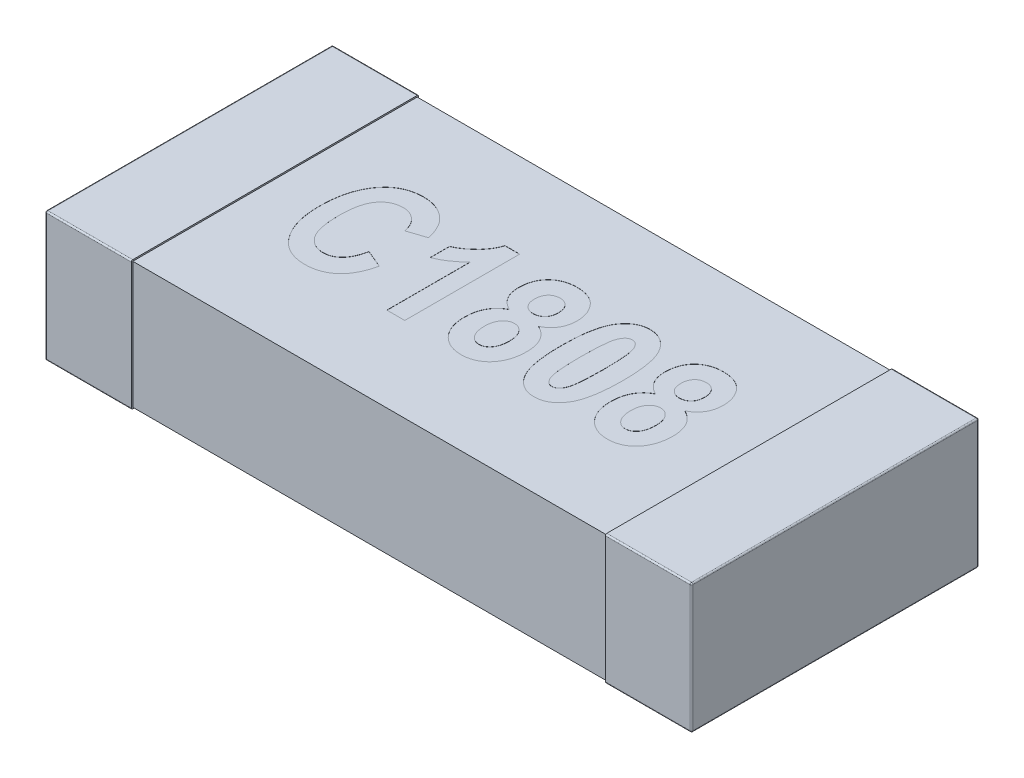
SolidWorks part; units mm, degrees
ref_plane "Front Plane" through (0, 0, 0) normal (0, 0, 1) x (1, 0, 0)
ref_plane "Top Plane" through (0, 0, 0) normal (0, 1, 0) x (1, 0, 0)
ref_plane "Right Plane" through (0, 0, 0) normal (1, 0, 0) x (0, 0, -1)
sketch "Sketch1" plane through (0, 0, 0) normal (0, 1, 0) x (1, 0, 0)
  line L0 (0, 0.15) -> (0, -0.15) construction
  line L1 (-2.25, 0) -> (0, 0) construction
  line L3 (-2.25, 1) -> (-1.65, 1)
  line L4 (-2.25, 1) -> (-2.25, -1)
  line L5 (-2.25, -1) -> (-1.65, -1)
  line L6 (-1.65, 1) -> (-1.65, -1)
  dimension "BANDWIDTH" = 0.6
  dimension "WIDTH" = 2
  dimension "LENGTH-HALF" = 2.25
extrude "THICKNESS" add sketch "Sketch1" along normal blind 0.9
fillet "Fillet1" radius 0.01 8 edges at (-2.25, 0, 0) (-1.95, 0, -1) (-2.25, 0.45, -1) (-1.95, 0, 1) (-2.25, 0.45, 1) (-2.25, 0.9, 0) (-1.95, 0.9, -1) (-1.95, 0.9, 1)
sketch "Sketch2" plane through (0, 0, 0) normal (1, 0, 0) x (0, 0, -1)
  line L0 (0, 0.9) -> (0, 0) construction
  line L1 (-0.99, 0.89) -> (0.99, 0.89)
  line L2 (-0.99, 0.89) -> (-0.99, 0.01)
  line L3 (-0.99, 0.01) -> (0.99, 0.01)
  line L4 (0.99, 0.89) -> (0.99, 0.01)
  line L5 (-0.99, 0.9) -> (0.99, 0.9) construction
  line L6 (-0.99, 0) -> (0.99, 0) construction
  line L7 (-1, 0.45) -> (1, 0.45) construction
  line L8 (-1, 0.89) -> (-1, 0.01) construction
  line L9 (1, 0.89) -> (1, 0.01) construction
  dimension "D1" = 0.01
  dimension "D2" = 0.01
extrude "Boss-Extrude2" add sketch "Sketch2" against normal up to surface (1.65 mm away) up to face at (-1.65, 0.45, 0)
mirror "Mirror3" about plane through (0, 0, 0) normal (1, 0, 0) of "Boss-Extrude2", "Fillet1", "THICKNESS"
sketch "Sketch3" plane through (0, 0.89, 0) normal (0, 1, 0) x (1, 0, 0)
  line L0 (-1.375, -0.4) -> (1.375, -0.4) construction
  line L1 (0, -0.495) -> (0, 0.495) construction
  line L2 (-0.495, 0) -> (0.495, 0) construction
  text T0 "<b>C1808</b>" font "Arial Narrow" height 0.8
  point P2 (0, -0.4)
  dimension "D1" = 2.75
  dimension "D2" = 0.4
extrude "Cut-Extrude1" cut sketch "Sketch3" against normal blind 0.001
